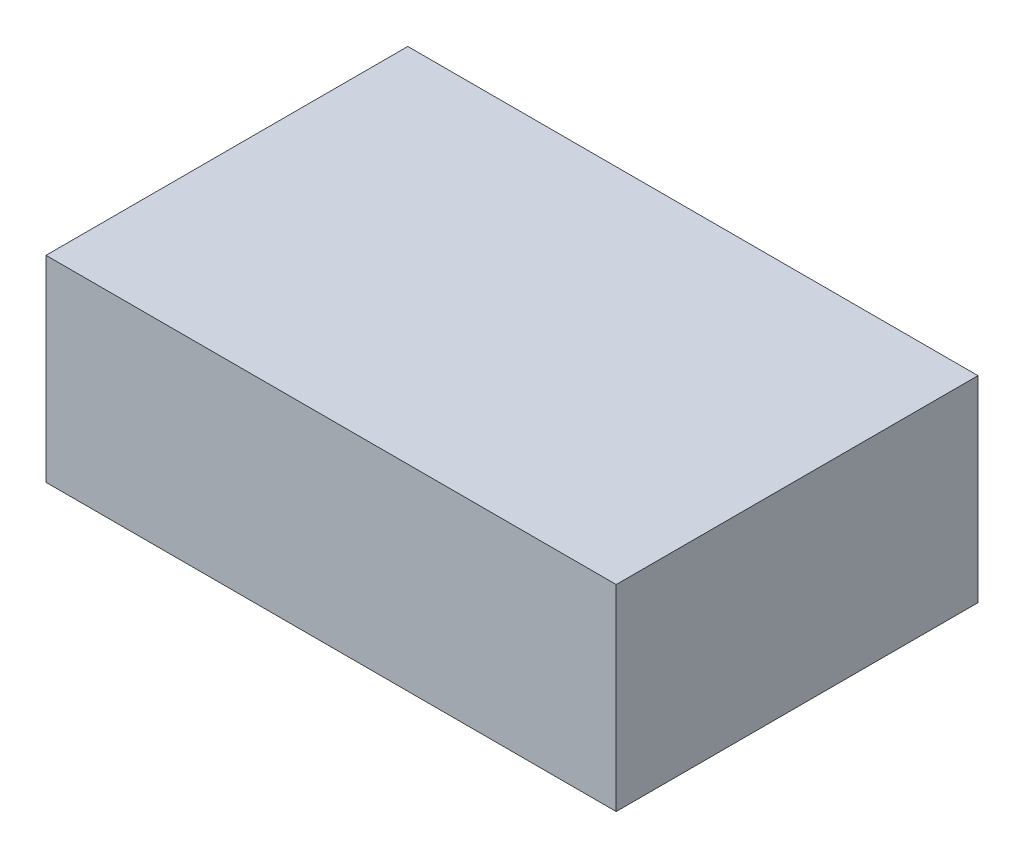
SolidWorks part; units mm, degrees
ref_plane "Ebene vorne" through (0, 0, 0) normal (0, 0, 1) x (1, 0, 0)
ref_plane "Ebene oben" through (0, 0, 0) normal (0, 1, 0) x (1, 0, 0)
ref_plane "Ebene rechts" through (0, 0, 0) normal (1, 0, 0) x (0, 0, -1)
sketch "Skizze1" plane through (0, 0, 0) normal (0, 1, 0) x (1, 0, 0)
  line L1 (-72.5, -46) -> (72.5, -46)
  line L2 (-72.5, -46) -> (-72.5, 46)
  line L3 (-72.5, 46) -> (72.5, 46)
  line L4 (72.5, -46) -> (72.5, 46)
  line L5 (-72.5, -46) -> (72.5, 46) construction
  line L6 (-72.5, 46) -> (72.5, -46) construction
  point P0 (0, 0)
  dimension "D1" = 145
  dimension "D2" = 92
extrude "Aufsatz-Linear austragen1" add sketch "Skizze1" along normal mid plane 50
